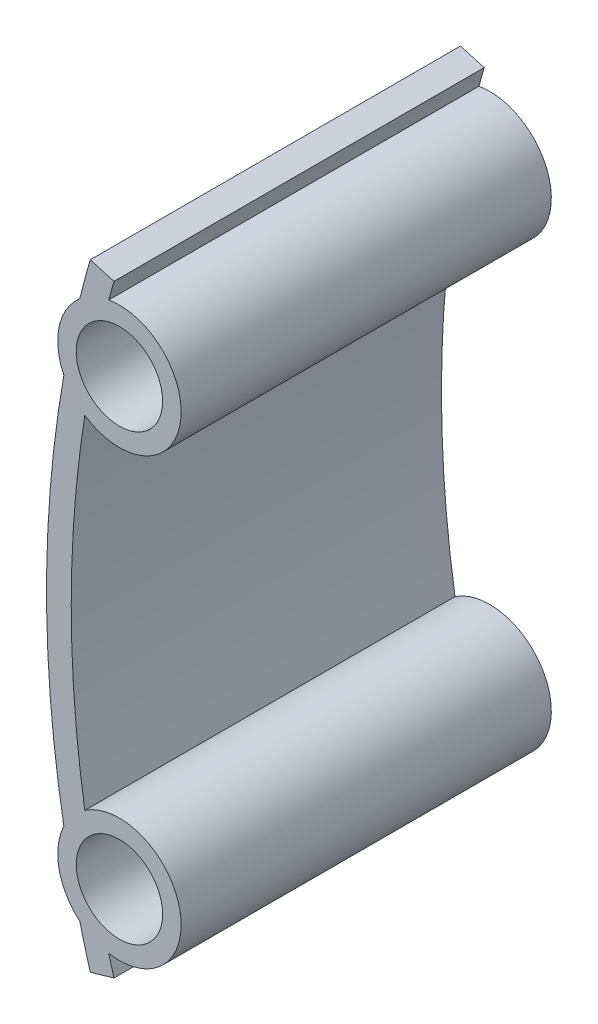
SolidWorks part; units mm, degrees
ref_plane "Front Plane" through (0, 0, 0) normal (0, 0, 1) x (1, 0, 0)
ref_plane "Top Plane" through (0, 0, 0) normal (0, 1, 0) x (1, 0, 0)
ref_plane "Right Plane" through (0, 0, 0) normal (1, 0, 0) x (0, 0, -1)
sketch "Sketch1" plane through (0, 0, 0) normal (0, 0, 1) x (1, 0, 0)
  line L0 (90, 0) -> (0, 0) construction
  line L1 (3.5419, 25) -> (3.5419, -25) construction
  line L2 (5.4632, 24.4444) -> (5.4632, -24.4444) construction
  line L3 (3.5419, 25) -> (5.4632, 24.4444)
  line L4 (5.4632, 24.4444) -> (90, 0) construction
  line L5 (3.5419, -25) -> (5.4632, -24.4444)
  line L6 (5.4632, -24.4444) -> (90, 0) construction
  line L7 (5.9048, 18) -> (5.9048, -18) construction
  arc A0 (3.5419, 25) -> (2.6868, 21.8268) centre (90, 0) ccw
  arc A1 (5.4632, 24.4444) -> (5.0384, 22.9244) centre (90, 0) ccw
  circle A2 centre (5.9048, 18) radius 3.5
  circle A3 centre (5.9048, -18) radius 3.5
  circle A4 centre (90, 0) radius 86 construction
  arc A5 (2.6868, 21.8268) -> (1.4023, 15.8257) centre (5.9048, 18) ccw
  arc A6 (1.4023, -15.8257) -> (2.6868, -21.8268) centre (5.9048, -18) ccw
  arc A7 (3.0986, 13.8617) -> (3.0986, -13.8617) centre (90, 0) ccw
  arc A8 (3.0986, 13.8617) -> (5.0384, 22.9244) centre (5.9048, 18) ccw
  arc A9 (1.4023, 15.8257) -> (1.4023, -15.8257) centre (90, 0) ccw
  circle A10 centre (5.9048, 18) radius 5 construction
  arc A11 (5.0384, -22.9244) -> (5.4632, -24.4444) centre (90, 0) ccw
  arc A12 (5.0384, -22.9244) -> (3.0986, -13.8617) centre (5.9048, -18) ccw
  arc A13 (2.6868, -21.8268) -> (3.5419, -25) centre (90, 0) ccw
  circle A14 centre (5.9048, -18) radius 5 construction
  circle A15 centre (90, 0) radius 90 construction
  dimension "D1" = 172
  dimension "D5" = 180
  dimension "D6" = 7
  dimension "D7" = 10
  dimension "D8" = 5
  dimension "D2" = 50
  dimension "D3" = 2
  dimension "D4" = 36
extrude "Boss-Extrude1" add sketch "Sketch1" along normal blind 30
